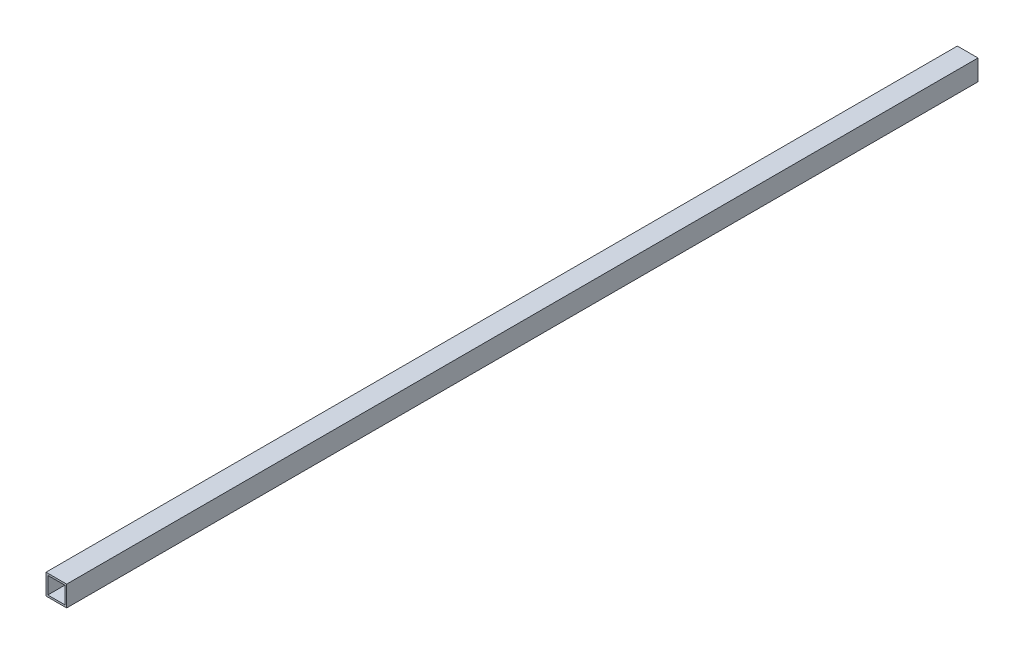
SolidWorks part; units mm, degrees
material "6061 Alloy"
ref_plane "Front Plane" through (0, 0, 0) normal (0, 0, 1) x (1, 0, 0)
ref_plane "Top Plane" through (0, 0, 0) normal (0, 1, 0) x (1, 0, 0)
ref_plane "Right Plane" through (0, 0, 0) normal (1, 0, 0) x (0, 0, -1)
sketch "Sketch1" plane through (0, 0, 0) normal (0, 0, 1) x (1, 0, 0)
  line L1 (-8.5, 8.5) -> (8.5, 8.5)
  line L2 (-8.5, 8.5) -> (-8.5, -8.5)
  line L3 (-8.5, -8.5) -> (8.5, -8.5)
  line L4 (8.5, 8.5) -> (8.5, -8.5)
  line L5 (-8.5, 8.5) -> (8.5, -8.5) construction
  line L6 (-8.5, -8.5) -> (8.5, 8.5) construction
  line L11 (-5.5475, 5.5475) -> (5.5475, -5.5475) construction
  line L12 (-5.5475, -5.5475) -> (5.5475, 5.5475) construction
  line L17 (-7, 7) -> (7, 7)
  line L18 (-7, 7) -> (-7, -7)
  line L19 (-7, -7) -> (7, -7)
  line L20 (7, 7) -> (7, -7)
  line L21 (-7, 7) -> (7, -7) construction
  line L22 (-7, -7) -> (7, 7) construction
  point P0 (0, 0)
  point P6 (0, 0)
  point P11 (0, 0)
  dimension "D1" = 17
  dimension "D2" = 17
  dimension "D3" = 1.5
extrude "Boss-Extrude1" add sketch "Sketch1" along normal blind 750
sketch "Sketch3" plane through (0, 8.5, 0) normal (0, 1, 0) x (1, 0, 0)
  line L0 (-8.5, -550) -> (8.5, -550)
  line L1 (-8.5, -750) -> (-8.5, 0) construction
  line L2 (8.5, -750) -> (8.5, 0) construction
  line L3 (-8.5, -375) -> (8.5, -375)
  line L4 (-8.5, -200) -> (8.5, -200)
  dimension "D1" = 175
  dimension "D2" = 175
